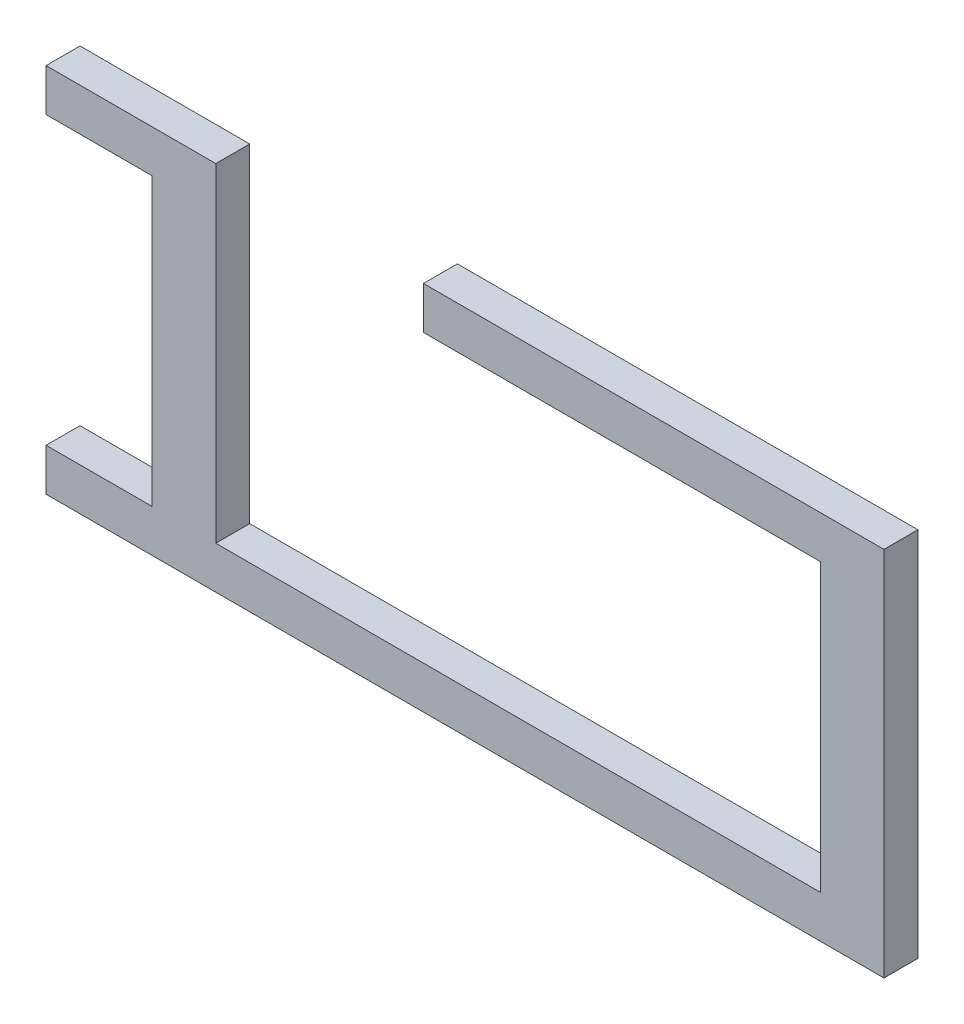
SolidWorks part; units mm, degrees
ref_plane "前视基准面" through (0, 0, 0) normal (0, 0, 1) x (1, 0, 0)
ref_plane "上视基准面" through (0, 0, 0) normal (0, 1, 0) x (1, 0, 0)
ref_plane "右视基准面" through (0, 0, 0) normal (1, 0, 0) x (0, 0, -1)
sketch "草图1" plane through (0, 0, 0) normal (0, 0, 1) x (1, 0, 0)
  line L0 (-3.1281, 3.2048) -> (46.8719, 3.2048) construction
  line L1 (14.6596, 3.2048) -> (36.3719, 3.2048)
  line L2 (14.6596, 3.2048) -> (14.6596, 1.2048)
  line L3 (14.6596, 1.2048) -> (33.3719, 1.2048)
  line L5 (1.8719, -12.2952) -> (-3.1281, -12.2952)
  line L7 (36.3719, 3.2048) -> (36.3719, -14.2952)
  line L9 (33.3719, 1.2048) -> (33.3719, -12.2952)
  line L11 (36.3719, -14.2952) -> (-3.1281, -14.2952)
  line L13 (33.3719, -12.2952) -> (4.8719, -12.2952)
  line L14 (-3.1281, -14.2952) -> (-3.1281, -12.2952)
  line L15 (-3.1281, 3.2048) -> (4.8719, 3.2048)
  line L16 (-3.1281, 3.2048) -> (-3.1281, 1.2048)
  line L17 (-3.1281, 1.2048) -> (1.8719, 1.2048)
  line L20 (4.8719, 3.2048) -> (4.8719, -12.2952)
  line L22 (1.8719, 1.2048) -> (1.8719, -12.2952)
  dimension "D1" = 2
  dimension "D2" = 3
  dimension "D3" = 2
  dimension "D4" = 39.5
  dimension "D5" = 3
  dimension "D6" = 5
extrude "凸台-拉伸1" add sketch "草图1" along normal blind 1.6
